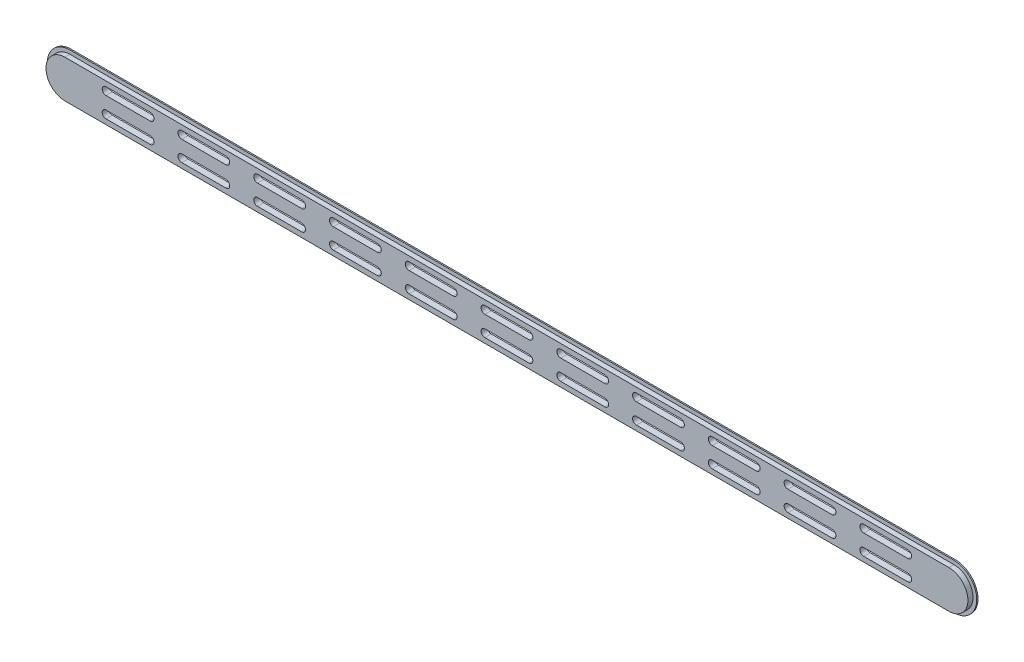
SolidWorks part; units mm, degrees
material "PVC Rigid"
ref_plane "Front Plane" through (0, 0, 0) normal (0, 0, 1) x (1, 0, 0)
ref_plane "Top Plane" through (0, 0, 0) normal (0, 1, 0) x (1, 0, 0)
ref_plane "Right Plane" through (0, 0, 0) normal (1, 0, 0) x (0, 0, -1)
sketch "Sketch3" plane through (0, 0, 0) normal (0, 0, 1) x (1, 0, 0)
  line L1 (-350, 18) -> (350, 18)
  line L2 (-350, -18) -> (350, -18)
  arc A0 (-350, 18) -> (-350, -18) centre (-350, 0) ccw
  arc A1 (350, 18) -> (350, -18) centre (350, 0) cw
  point P4 (0, 0)
  point P8 (0, 18)
  point P11 (0, -18)
extrude "Boss-Extrude4" add sketch "Sketch3" along normal blind 1 contours A0 L2 A1 L1
sketch "Sketch4" plane through (0, 0, 1) normal (0, 0, 1) x (1, 0, 0)
  line L1 (-350, 15) -> (350, 15)
  line L2 (-350, -15) -> (350, -15)
  arc A0 (350, 15) -> (350, -15) centre (350, 0) cw
  arc A1 (-350, -15) -> (-350, 15) centre (-350, 0) cw
  point P4 (0, 0)
  point P8 (0, 15)
  point P10 (0, -15)
extrude "Boss-Extrude5" add sketch "Sketch4" along normal blind 4 contours L1 A0 L2 A1
sketch "Sketch5" plane through (0, 0, 5) normal (0, 0, 1) x (1, 0, 0)
  line L0 (-365, 0) -> (365, 0) construction
  line L2 (-317.5, 11) -> (-282.5, 11)
  line L3 (-317.5, 5) -> (-282.5, 5)
  arc A0 (350, -15) -> (350, 15) centre (350, 0) ccw construction
  arc A1 (-282.5, 5) -> (-282.5, 11) centre (-282.5, 8) ccw
  arc A2 (-317.5, 5) -> (-317.5, 11) centre (-317.5, 8) cw
  point P0 (-300, 8)
  point P7 (0, 0)
  point P13 (-300, 11)
  point P16 (-300, 8)
  point P19 (-300, 5)
  dimension "D1" = 50
  dimension "D2" = 8
extrude "Cut-Extrude3" cut sketch "Sketch5" against normal through all contours L2 A1 L3 A2
pattern_linear "LPattern1" count 11 spacing 60 along (1, 0, 0) of "Cut-Extrude3"
mirror "Mirror1" about plane through (0, 0, 0) normal (0, 1, 0) of "LPattern1", "Cut-Extrude3"
